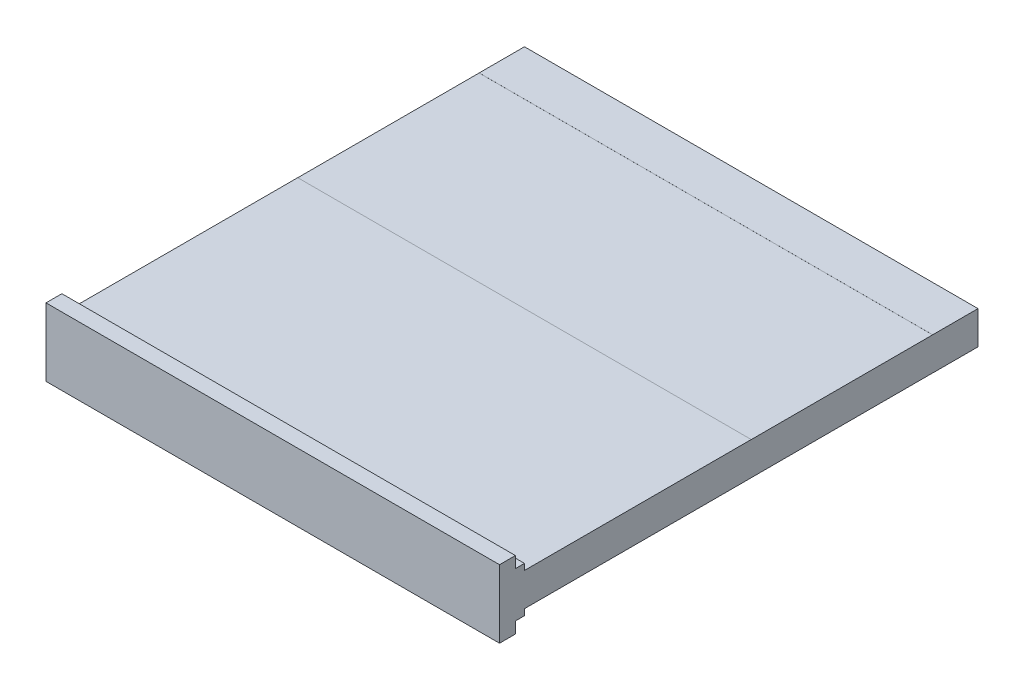
SolidWorks part; units mm, degrees
ref_plane "Top Plane" through (0, 0, 0) normal (0, 0, 1) x (1, 0, 0)
ref_plane "Front Plane" through (0, 0, 0) normal (0, 1, 0) x (1, 0, 0)
ref_plane "Right Plane" through (0, 0, 0) normal (1, 0, 0) x (0, 0, -1)
sketch "Sketch1" plane through (0, 0, 0) normal (0, 0, 1) x (1, 0, 0)
  line L1 (0, 0) -> (1, 0)
  line L2 (0, 0) -> (0, 0.0729)
  line L3 (0, 0.0729) -> (1, 0.0729)
  line L4 (1, 0) -> (1, 0.0729)
  dimension "D1" = 0.0729
  dimension "D2" = 1
extrude "Boss-Extrude1" add sketch "Sketch1" along normal blind 1 contours L3 L4 L1 L2
sketch "Sketch2" plane through (0, 0, 1) normal (0, 0, 1) x (1, 0, 0)
  line L0 (0, 0) -> (0, 0.0729) construction
  line L1 (0, 0.0864) -> (1, 0.0864)
  line L2 (0, 0.0864) -> (0, -0.0136)
  line L3 (0, -0.0136) -> (1, -0.0136)
  line L4 (1, 0.0864) -> (1, -0.0136)
  line L5 (1, 0) -> (1, 0.0729) construction
  line L6 (0, 0.0364) -> (0.5, 0.0364) construction
  line L7 (0.5, 0.0729) -> (0.5, 0) construction
  line L8 (0, 0.0729) -> (1, 0.0729) construction
  line L9 (0, 0) -> (1, 0) construction
  point P16 (0.5, 0.0364)
  dimension "D1" = 0.1
extrude "Boss-Extrude2" add sketch "Sketch2" along normal blind 0.02
sketch "Sketch3" plane through (0, 0, 1.02) normal (0, 0, 1) x (1, 0, 0)
  line L0 (0, 0.0864) -> (0, -0.0136) construction
  line L1 (0, 0.1114) -> (1, 0.1114)
  line L2 (0, 0.1114) -> (0, -0.0386)
  line L3 (0, -0.0386) -> (1, -0.0386)
  line L4 (1, 0.1114) -> (1, -0.0386)
  line L7 (0.5, 0.0864) -> (0.5, -0.0136) construction
  line L8 (1, 0.0864) -> (0, 0.0864) construction
  line L9 (0, -0.0136) -> (1, -0.0136) construction
  line L10 (0.5, 0.0364) -> (1, 0.0364) construction
  line L11 (1, -0.0136) -> (1, 0.0864) construction
  dimension "D1" = 0.15
extrude "Boss-Extrude3" add sketch "Sketch3" along normal blind 0.035
sketch "Sketch4" plane through (0, 0, 0) normal (0, -1, 0) x (1, 0, 0)
  line L0 (1, 1) -> (1, 0) construction
  line L1 (0, 0) -> (1, 0)
  line L2 (0, 0) -> (0, 0.1)
  line L3 (0, 0.1) -> (1, 0.1)
  line L4 (1, 0) -> (1, 0.1)
  line L6 (0, 1) -> (1, 1)
  line L7 (0, 1) -> (0, 0.5)
  line L8 (0, 0.5) -> (1, 0.5)
  line L9 (1, 1) -> (1, 0.5)
  dimension "D1" = 0.1
extrude "Boss-Extrude4" add sketch "Sketch4" along normal blind 0.0001
sketch "Sketch6" plane through (0, 0.0729, 0) normal (0, 1, 0) x (1, 0, 0)
  line L0 (0, -1) -> (0, 0) construction
  line L1 (1, 0) -> (0, 0)
  line L2 (1, 0) -> (1, -0.1)
  line L3 (1, -0.1) -> (0, -0.1)
  line L4 (0, 0) -> (0, -0.1)
  line L6 (1, -1) -> (0, -1)
  line L7 (1, -1) -> (1, -0.5)
  line L8 (1, -0.5) -> (0, -0.5)
  line L9 (0, -1) -> (0, -0.5)
  dimension "D1" = 0.1
extrude "Boss-Extrude5" add sketch "Sketch6" along normal blind 0.0001
